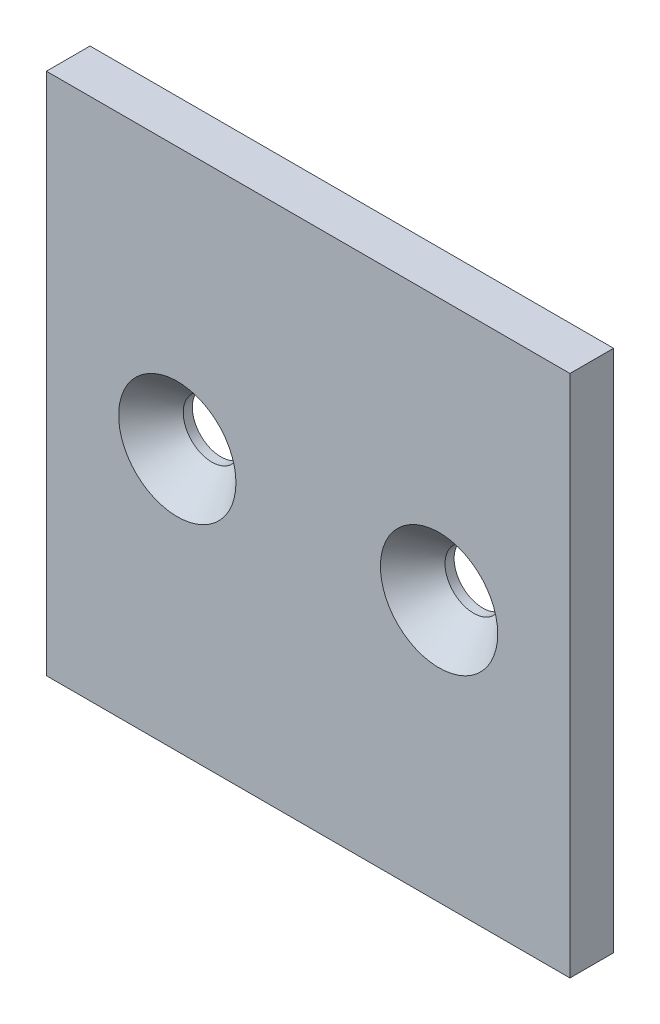
SolidWorks part; units mm, degrees
ref_plane "Front Plane" through (0, 0, 0) normal (0, 0, 1) x (1, 0, 0)
ref_plane "Top Plane" through (0, 0, 0) normal (0, 1, 0) x (1, 0, 0)
ref_plane "Right Plane" through (0, 0, 0) normal (1, 0, 0) x (0, 0, -1)
sketch "Sketch1" plane through (0, 0, 0) normal (0, 0, 1) x (1, 0, 0)
  line L0 (0, 0) -> (0, 76.2)
  line L1 (19.05, 38.1) -> (57.15, 38.1) construction
  line L4 (76.2, 76.2) -> (0, 76.2)
  line L5 (76.2, 0) -> (0, 0)
  line L7 (76.2, 76.2) -> (76.2, 0)
  circle A0 centre (19.05, 38.1) radius 4.1656
  circle A1 centre (57.15, 38.1) radius 4.1656
  dimension "D1" = 38.1
  dimension "E" = 8.3312
  dimension "D2" = 19.05
  dimension "C" = 76.2
  dimension "D3" = 38.1
  dimension "B" = 76.2
extrude "Boss-Extrude1" add sketch "Sketch1" along normal mid plane 6.35
sketch "Sketch2" plane through (0, 0, 3.175) normal (0, 0, 1) x (1, 0, 0)
  circle A0 centre (19.05, 38.1) radius 4.1656 construction
  circle A1 centre (19.05, 38.1) radius 4.1656
  circle A2 centre (57.15, 38.1) radius 4.1656 construction
  circle A3 centre (57.15, 38.1) radius 4.1656
extrude "Cut-Extrude1" cut sketch "Sketch2" along normal through all draft 41 from offset 5.0292
